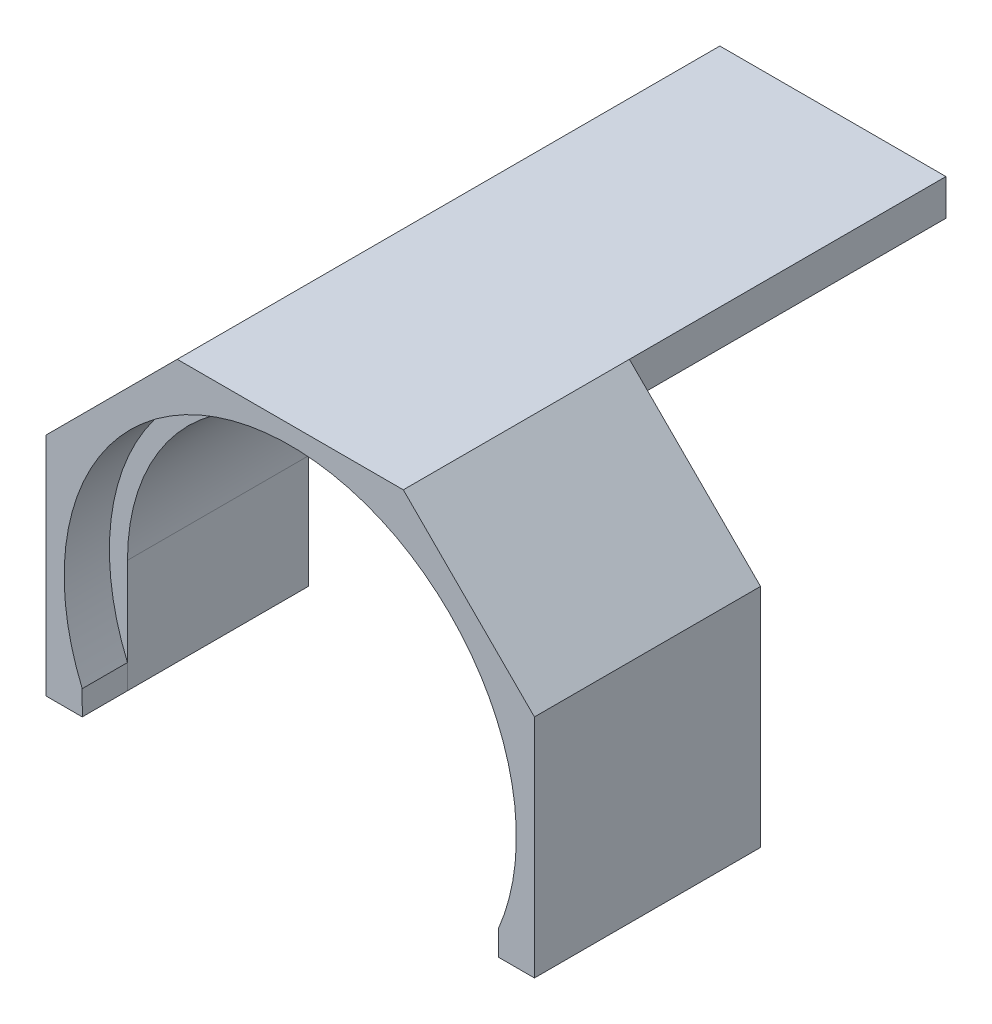
SolidWorks part; units mm, degrees
ref_plane "前视基准面" through (0, 0, 0) normal (0, 0, 1) x (1, 0, 0)
ref_plane "上视基准面" through (0, 0, 0) normal (0, 1, 0) x (1, 0, 0)
ref_plane "右视基准面" through (0, 0, 0) normal (1, 0, 0) x (0, 0, -1)
sketch "草图1" plane through (0, 0, 0) normal (0, 0, 1) x (1, 0, 0)
  line L0 (-39.8017, 0) -> (0, 0) construction
  line L1 (0, 0) -> (0, 40.2975) construction
  line L3 (-25, 4) -> (25, 4)
  line L4 (-25, 4) -> (-25, -4)
  line L5 (-25, -4) -> (25, -4)
  line L6 (25, 4) -> (25, -4)
  dimension "D1" = 50
  dimension "D2" = 25
  dimension "D3" = 8
  dimension "D4" = 4
sketch "草图2" plane through (0, 0, 0) normal (1, 0, 0) x (0, 0, -1)
  line L0 (0, 55.2983) -> (-110, 55.2983)
  line L1 (0, 4) -> (0, -4) construction
  line L2 (0, 4) -> (0, -4) construction
sweep "扫描1" add profiles "草图1" path "草图2"
sketch "草图4" plane through (0, 0, 110) normal (0, 0, 1) x (1, 0, 0)
  line L0 (0, -4) -> (0, -65.5134) construction
  line L4 (-25, -4) -> (25, -4) construction
  line L5 (-44.7277, -50) -> (-40, -50) construction
  line L6 (-54, -25) -> (-25, 4)
  line L8 (-54, -25) -> (-54, -75)
  line L14 (54, -25) -> (54, -75)
  line L15 (-25, 4) -> (25, 4)
  line L16 (25, 4) -> (54, -25)
  line L17 (-36, -50) -> (36, -50) construction
  line L19 (-46, -50) -> (-46, -75)
  line L20 (46, -50) -> (46, -75)
  line L21 (-54, -75) -> (-46, -75)
  line L22 (46, -75) -> (54, -75)
  arc A4 (46, -50) -> (-46, -50) centre (0, -50) ccw
  dimension "D2" = 50
  dimension "D1" = 25
  dimension "D3" = 8
  dimension "D4" = 8
  dimension "D5" = 50
extrude "凸台-拉伸1" add sketch "草图4" against normal blind 40
sketch "草图5" plane through (0, 0, 110) normal (0, 0, 1) x (1, 0, 0)
  line L0 (-46.0047, -69.585) -> (-46, -75)
  line L1 (-46, -75) -> (-54, -75)
  line L2 (-54, -75) -> (-54, -25)
  line L3 (-54, -25) -> (-25, 4)
  line L4 (-25, 4) -> (25, 4)
  line L5 (25, 4) -> (54, -25)
  line L6 (54, -25) -> (54, -75)
  line L7 (54, -75) -> (54, -25) construction
  line L8 (46, -75) -> (54, -75) construction
  line L9 (54, -75) -> (46, -75)
  line L10 (46, -50) -> (46, -75) construction
  line L11 (46, -69.5959) -> (46, -75)
  arc A0 (46, -69.5959) -> (-46.0047, -69.585) centre (0, -50) ccw
  point P3 (-46.0047, -69.585)
  point P24 (46, -69.5959)
extrude "凸台-拉伸2" add sketch "草图5" along normal blind 10
